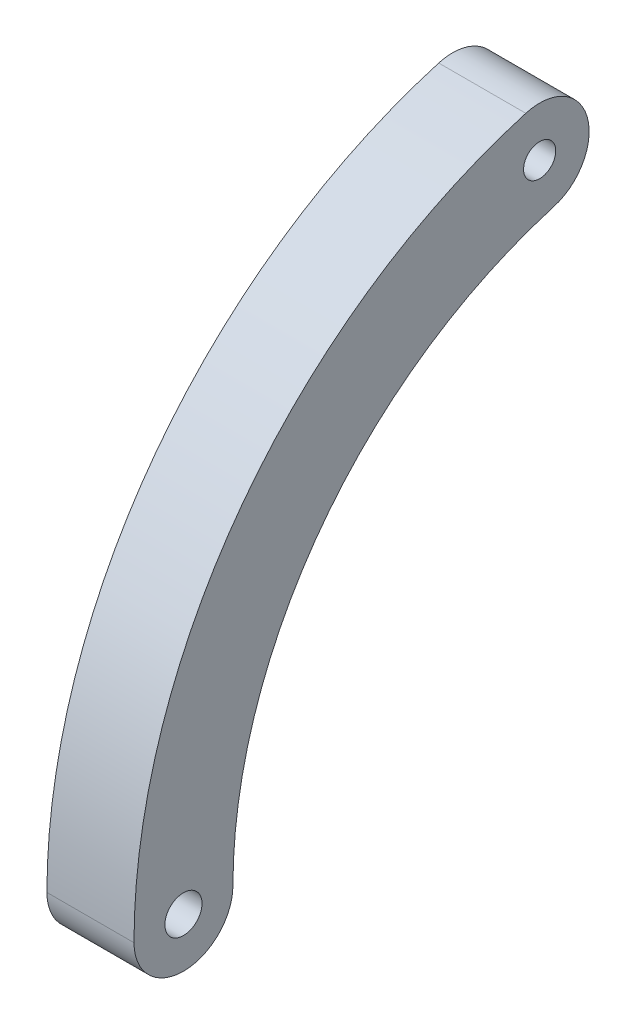
SolidWorks part; units mm, degrees
material "ABS"
ref_plane "Front Plane" through (0, 0, 0) normal (0, 0, 1) x (1, 0, 0)
ref_plane "Top Plane" through (0, 0, 0) normal (0, 1, 0) x (1, 0, 0)
ref_plane "Right Plane" through (0, 0, 0) normal (1, 0, 0) x (0, 0, -1)
sketch "Esquisse1" plane through (0, 0, 0) normal (1, 0, 0) x (0, 0, -1)
  arc A0 (-28.575, 0) -> (-8.001, 27.432) centre (0, 0) cw
  arc A1 (-34.925, 0) -> (-9.779, 33.528) centre (0, 0) cw
  arc A2 (-34.925, 0) -> (-28.575, 0) centre (-31.75, 0) ccw
  arc A3 (-8.001, 27.432) -> (-9.779, 33.528) centre (-8.89, 30.48) ccw
  circle A4 centre (-31.75, 0) radius 1.1906
  circle A5 centre (-8.89, 30.48) radius 1.0319
  dimension "D1" = 3.175
  dimension "D4" = 2.3812
  dimension "D5" = 2.0638
  dimension "D2" = 38.1
  dimension "D3" = 31.75
extrude "Boss.-Extru.1" add sketch "Esquisse1" along normal blind 5.588
